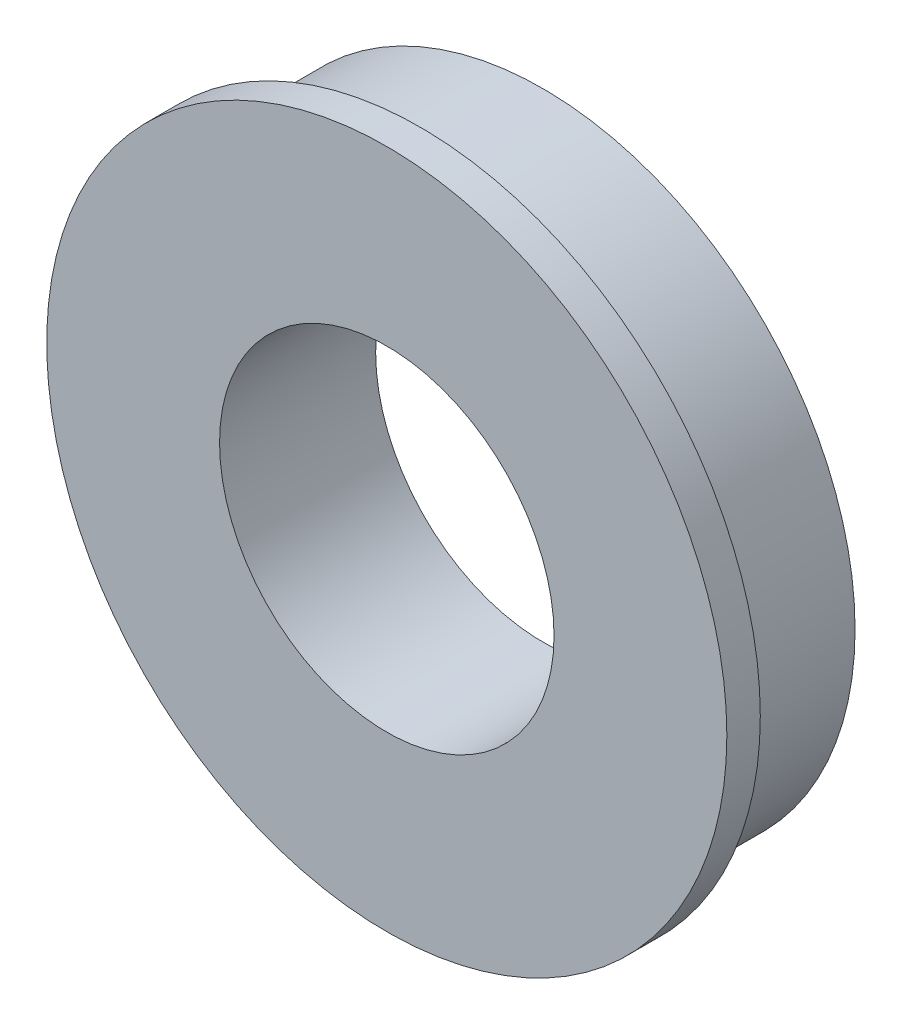
SolidWorks part; units mm, degrees
material "合金钢"
ref_plane "前视基准面" through (0, 0, 0) normal (0, 0, 1) x (1, 0, 0)
ref_plane "上视基准面" through (0, 0, 0) normal (0, 1, 0) x (1, 0, 0)
ref_plane "右视基准面" through (0, 0, 0) normal (1, 0, 0) x (0, 0, -1)
sketch "草图1" plane through (0, 0, 0) normal (0, 0, 1) x (1, 0, 0)
  circle A0 centre (0, 0) radius 14
  dimension "D1" = 28
extrude "凸台-拉伸1" add sketch "草图1" along normal blind 5.5
sketch "草图2" plane through (0, 0, 5.5) normal (0, 0, 1) x (1, 0, 0)
  circle A0 centre (0, 0) radius 15.25
  dimension "D1" = 30.5
extrude "凸台-拉伸2" add sketch "草图2" along normal blind 1.5
sketch "草图3" plane through (0, 0, 0) normal (0, 0, -1) x (-1, 0, 0)
  circle A0 centre (0, 0) radius 7.5
  dimension "D1" = 15
extrude "切除-拉伸1" cut sketch "草图3" against normal up to next
